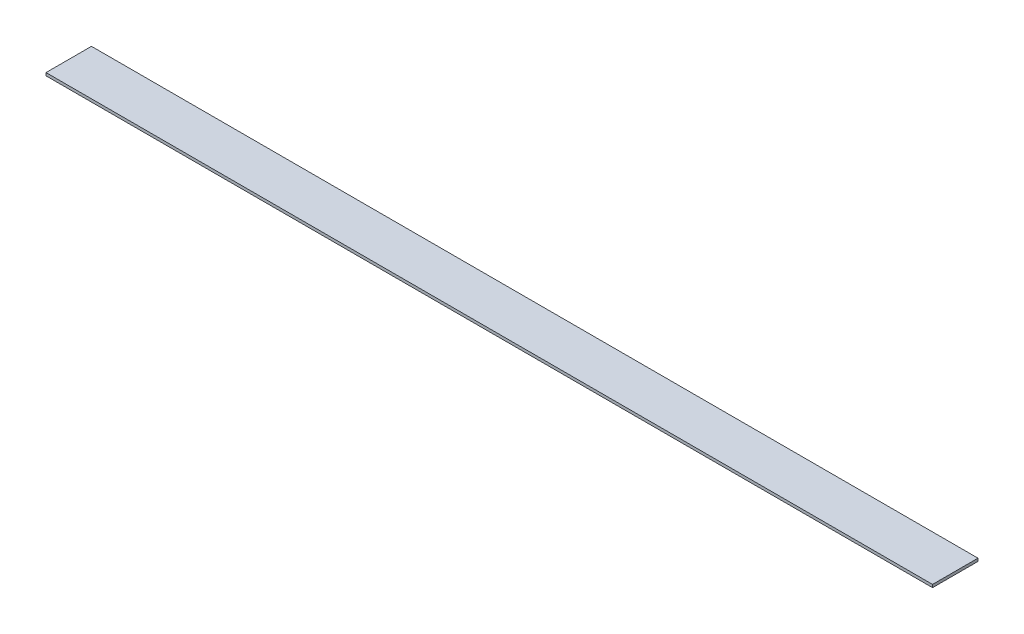
SolidWorks part; units mm, degrees
material "Very Low Density PE (SS)"
ref_plane "Front Plane" through (0, 0, 0) normal (0, 0, 1) x (1, 0, 0)
ref_plane "Top Plane" through (0, 0, 0) normal (0, 1, 0) x (1, 0, 0)
ref_plane "Right Plane" through (0, 0, 0) normal (1, 0, 0) x (0, 0, -1)
sketch "Sketch1" plane through (0, 0, 0) normal (0, 1, 0) x (1, 0, 0)
  line L1 (495.3, -25.4) -> (-495.3, -25.4)
  line L2 (495.3, -25.4) -> (495.3, 25.4)
  line L3 (495.3, 25.4) -> (-495.3, 25.4)
  line L4 (-495.3, -25.4) -> (-495.3, 25.4)
  line L5 (495.3, -25.4) -> (-495.3, 25.4) construction
  line L6 (495.3, 25.4) -> (-495.3, -25.4) construction
  point P0 (0, 0)
  dimension "D1" = 990.6
  dimension "D2" = 50.8
extrude "Boss-Extrude1" add sketch "Sketch1" along normal blind 3.175
